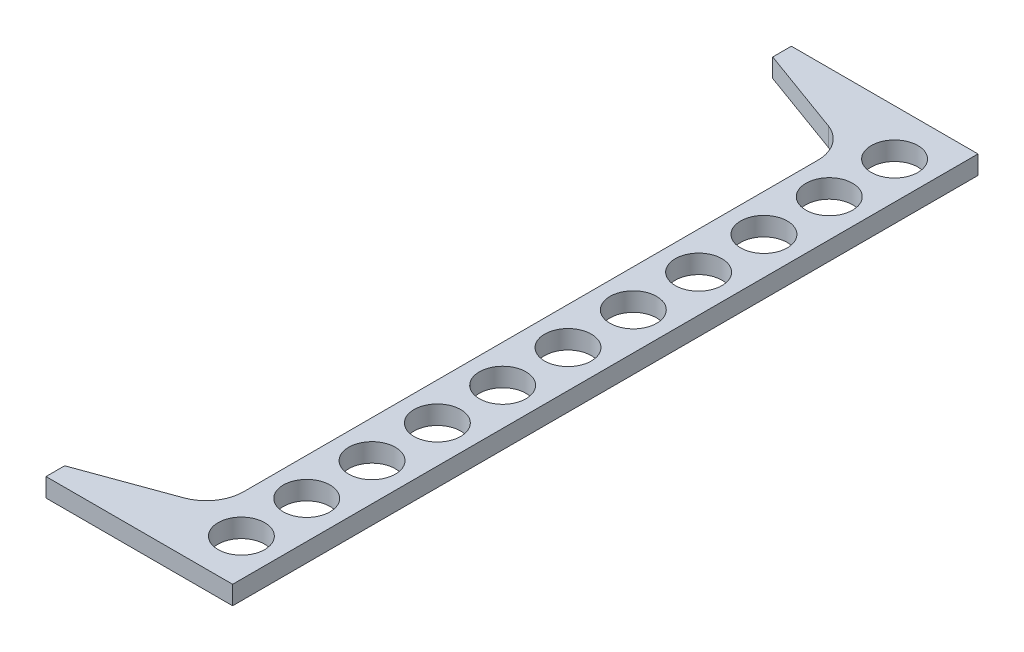
SolidWorks part; units mm, degrees
material "6061-T6 (SS)"
ref_plane "Front Plane" through (0, 0, 0) normal (0, 0, 1) x (1, 0, 0)
ref_plane "Top Plane" through (0, 0, 0) normal (0, 1, 0) x (1, 0, 0)
ref_plane "Right Plane" through (0, 0, 0) normal (1, 0, 0) x (0, 0, -1)
sketch "Sketch1" plane through (0, 0, 0) normal (0, 0, 1) x (1, 0, 0)
  line L1 (0, 0) -> (63.5, 0)
  line L2 (0, 0) -> (0, 6.35)
  line L3 (0, 6.35) -> (63.5, 6.35)
  line L4 (63.5, 0) -> (63.5, 6.35)
  dimension "D2" = 63.5
  dimension "D3" = 6.35
extrude "Boss-Extrude1" add sketch "Sketch1" along normal mid plane 253.619
sketch "Sketch2" plane through (0, 6.35, 0) normal (0, 1, 0) x (1, 0, 0)
  line L0 (0, 120.4595) -> (38.1, 106.5922)
  line L1 (0, -126.8095) -> (0, 126.8095) construction
  line L2 (38.1, 106.5922) -> (38.1, -106.5922)
  line L3 (38.1, -106.5922) -> (0, -120.4595)
  line L4 (0, 126.8095) -> (63.5, 126.8095) construction
  line L5 (0, -126.8095) -> (63.5, -126.8095) construction
  line L6 (63.5, -126.8095) -> (63.5, 126.8095) construction
  dimension "D1" = 6.35
  dimension "D2" = 6.35
  dimension "D5" = 25.4
  dimension "D3" = 20
  dimension "D4" = 20
extrude "Cut-Extrude1" cut sketch "Sketch2" against normal through all and the other way through all flip side to cut
fillet "Fillet1" radius 12.7 2 edges at (38.1, 3.175, 106.5922) (38.1, 3.175, -106.5922)
hole_wizard "5/8 (0.625) Diameter Hole1" positions "Sketch3" profile "Sketch4" hole size "5/8" standard "ANSI Inch"
sketch "Sketch3" plane through (0, 6.35, 0) normal (0, 1, 0) x (1, 0, 0)
  line L0 (63.5, -126.8095) -> (63.5, 126.8095) construction
  point P0 (50.8, 0)
  point P11 (63.5, 0)
  dimension "D1" = 12.7
sketch "Sketch4" plane through (50.8, 6.35, 0) normal (1, 0, 0) x (0, 0, 1)
  line L0 (0, 0) -> (0, 23.8193)
  line L1 (0, 23.8193) -> (7.9375, 19.05)
  line L2 (7.9375, 19.05) -> (7.9375, 0)
  line L5 (7.9375, 0) -> (0, 0)
  line L10 (0, 23.8193) -> (-7.9375, 19.05) construction
  line L11 (0, -6.35) -> (0, 107.95) construction
  dimension "Hole Dia." = 15.875
  dimension "Hole Depth" = 19.05
  dimension "Drill Angle" = 118
pattern_linear "LPattern1" count 6 spacing 22.225 along (0, 0, -1) of "5/8 (0.625) Diameter Hole1"
mirror "Mirror1" about plane through (0, 0, 0) normal (0, 0, 1) of "LPattern1"
equation "\"D4@Sketch2\"=\"D3@Sketch2\""
